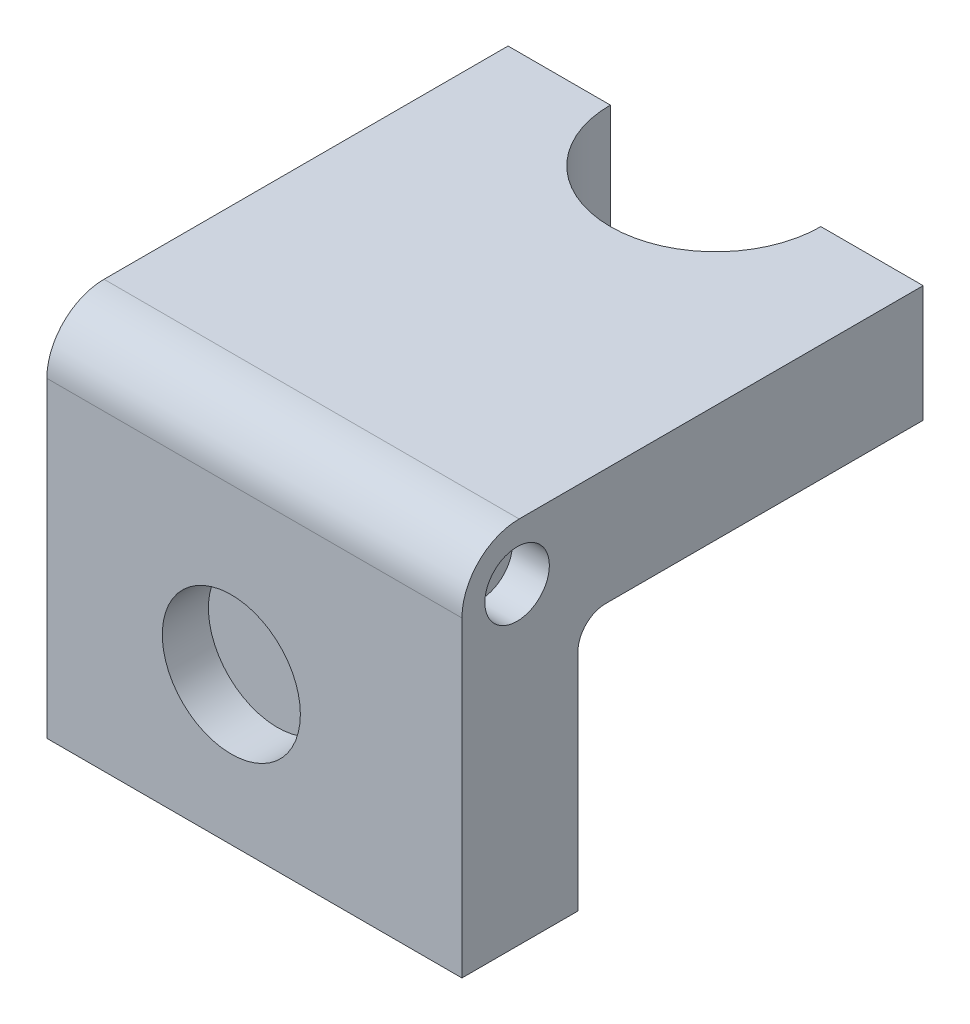
SolidWorks part; units mm, degrees
material "1060 Alloy"
ref_plane "Front Plane" through (0, 0, 0) normal (0, 0, 1) x (1, 0, 0)
ref_plane "Top Plane" through (0, 0, 0) normal (0, 1, 0) x (1, 0, 0)
ref_plane "Right Plane" through (0, 0, 0) normal (1, 0, 0) x (0, 0, -1)
sketch "Sketch1" plane through (0, 0, 0) normal (0, 0, 1) x (1, 0, 0)
  line L1 (0, 0) -> (57.15, 0)
  line L2 (0, 0) -> (0, 50.8)
  line L3 (0, 50.8) -> (57.15, 50.8)
  line L4 (57.15, 0) -> (57.15, 50.8)
  dimension "D1" = 50.8
  dimension "D2" = 57.15
extrude "Boss-Extrude1" add sketch "Sketch1" along normal blind 63.5
sketch "Sketch2" plane through (0, 0, 63.5) normal (0, 0, 1) x (1, 0, 0)
  circle A0 centre (25.4, 20.32) radius 9.5061
  dimension "D1" = 25.4
  dimension "D2" = 20.32
extrude "Cut-Extrude1" cut sketch "Sketch2" against normal blind 6.35
fillet "Fillet1" radius 7.874 1 edges at (28.575, 50.8, 63.5)
sketch "Sketch3" plane through (57.15, 0, 0) normal (1, 0, 0) x (0, 0, -1)
  line L1 (0, 0) -> (-47.5246, 0)
  line L2 (0, 0) -> (0, 34.7459)
  line L3 (0, 34.7459) -> (-47.5246, 34.7459)
  line L4 (-47.5246, 0) -> (-47.5246, 34.7459)
extrude "Cut-Extrude2" cut sketch "Sketch3" against normal blind 57.15
fillet "Fillet2" radius 3.81 1 edges at (28.575, 34.7459, 47.5246)
sketch "Sketch4" plane through (57.15, 0, 0) normal (1, 0, 0) x (0, 0, -1)
  circle A0 centre (-55.9066, 43.18) radius 4.4422
  dimension "D1" = 8.382
  dimension "D2" = 7.62
extrude "Cut-Extrude3" cut sketch "Sketch4" against normal blind 5.08
sketch "Sketch5" plane through (0, 50.8, 0) normal (0, 1, 0) x (1, 0, 0)
  line L1 (57.15, 0) -> (0, 0) construction
  line L2 (14.0819, 0) -> (43.0681, 0)
  arc A0 (43.0681, 0) -> (14.0819, 0) centre (28.575, 0) cw
sketch "Sketch6" plane through (0, 50.8, 0) normal (0, 1, 0) x (1, 0, 0)
extrude "Cut-Extrude4" cut sketch "Sketch5" against normal blind 25.4 contours L2 A0
